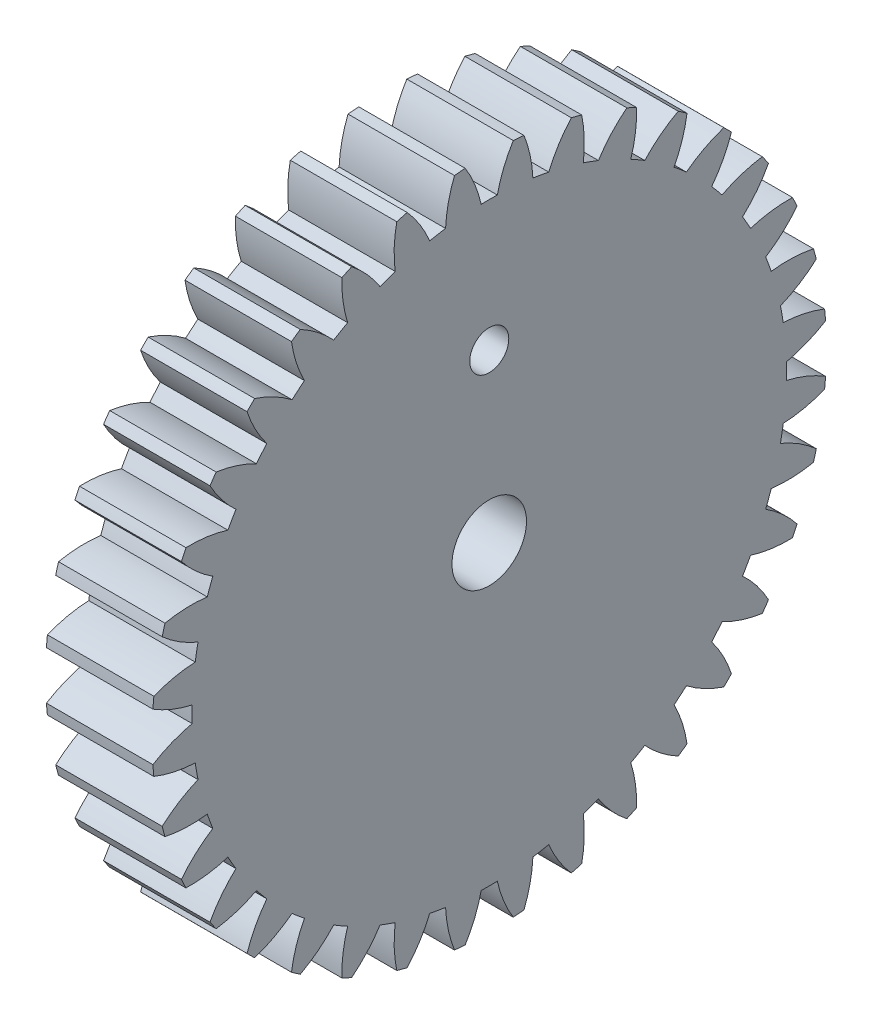
SolidWorks part; units mm, degrees
ref_plane "Plane1" through (0, 0, 0) normal (0, 0, 1) x (1, 0, 0)
ref_plane "Plane2" through (0, 0, 0) normal (0, 1, 0) x (1, 0, 0)
ref_plane "Plane3" through (0, 0, 0) normal (1, 0, 0) x (0, 0, -1)
sketch "HoldingSke" plane through (0, 0, 0) normal (0, 1, 0) x (1, 0, 0)
  line L0 (0, 0) -> (0.809, -0.5878)
  line L1 (-15, 0) -> (100, 0) construction
  line L2 (0, 0) -> (-2.1039, 2.3779)
  line L3 (0, 0) -> (-11.863, 4.5341)
  line L4 (0, 0) -> (6.9867, 5.0761)
  line L5 (0, 0) -> (-46.8476, -17.4728)
  line L6 (0, 0) -> (-5.8027, -3.9151)
  line L7 (-2.1039, 2.3779) -> (8.6586, 51.2059)
  line L8 (-76.2, 54.61) -> (-76.1, 54.61)
  line L9 (-71.009, 38.7566) -> (-53.1078, 45.2721)
  line L10 (-76.2, 71.12) -> (104.1128, 71.12)
  line L11 (0, 0) -> (-7, 0)
  line L12 (-76.2, 101.6) -> (-76.162, 101.6)
  line L13 (24.9733, 27.94) -> (52.9518, 28.4284)
  line L14 (24.9733, 27.94) -> (24.9743, 27.94)
  line L15 (24.9733, 27.94) -> (100.4006, 29.5858)
  line L16 (-63.627, -1) -> (-12.827, -1)
  circle A0 centre (0, 0) radius 0.4
  circle A1 centre (0, 0) radius 16.749
  circle A2 centre (0, 0) radius 37.5
  circle A3 centre (0, 0) radius 0.4
  dimension "MHD" = 33.498
  dimension "Hub_dia" = 75
  dimension "Bore" = 0.8
  dimension "MBD" = 0.8
  dimension "Num_teeth" = 36
  dimension "Pitch_radius" = 180.3128
  dimension "Pitch" = 1
  dimension "Width" = 7
  dimension "Overall_len" = 50
  dimension "Show_teeth" = 36
  dimension "Thickness" = 7
  dimension "OAL" = 50.0001
  dimension "T_dim" = 0.1
  dimension "Ap" = 20
  dimension "H" = 19.05
  dimension "Backlash" = 0.038
  dimension "Addendum_fac" = 1
  dimension "Dedendum_fac" = 1.25
  dimension "Clearance_fac" = 0.25
  dimension "Dedendum_add" = 0.001
  dimension "Module" = 1
sketch "BasProSke" plane through (0, 0, 0) normal (0, 1, 0) x (1, 0, 0)
  line L0 (-10, 0) -> (60, 0) construction
  line L1 (0, 0) -> (0, 19)
  line L2 (0, 0) -> (7, 0)
  line L3 (7, 0) -> (7, 19)
  line L4 (7, 19) -> (0, 19)
  dimension "Diameter" = 38
  dimension "Thickness" = 7
revolve "Base-Revolve" add sketch "BasProSke" angle 360 about L0
sketch "TooCutSke" plane through (0, 0, 0) normal (1, 0, 0) x (0, 0, -1)
  line L1 (0, 0) -> (0, 107) construction
  line L2 (0, 0) -> (-0.8516, 17.9798) construction
  line L3 (0, 0) -> (-3.1351, 35.8344) construction
  line L4 (-0.8516, 17.9798) -> (-1.5676, 17.9172) construction
  arc A0 (0.4547, 16.7428) -> (-0.4547, 16.7428) centre (0, 0) ccw
  arc A1 (1.3689, 18.9761) -> (-1.3689, 18.9761) centre (0, 0) ccw
  circle A2 centre (0, 0) radius 18 construction
  circle A3 centre (0, 0) radius 16.9145 construction
  arc A4 (-0.4547, 16.7428) -> (-1.3689, 18.9761) centre (-7.4808, 15.1702) ccw
  arc A5 (1.3689, 18.9761) -> (0.4547, 16.7428) centre (7.4808, 15.1702) ccw
  dimension "Root_dia" = 33.498
  dimension "Overcut_dia" = 38.0508
  dimension "Pitch_dia" = 36
  dimension "Base_dia" = 33.8289
  dimension "Flank_rad" = 7.2
  dimension "Half_ang" = 5
  dimension "Half_CT" = 0.7186
extrude "ToothCut" cut sketch "TooCutSke" along normal through all
fillet "Breaks" [suppressed] radius 0.02
fillet "RootFillets" [suppressed] radius 0.251
pattern_circular "TeethCuts" count 36 every 10 about axis through (-10, 0, 0) along (1, 0, 0) of "ToothCut", "RootFillets", "Breaks"
sketch "HubNeaOneSke" plane through (0, 0, 0) normal (-1, 0, 0) x (0, 0, 1)
  circle A0 centre (0, 0) radius 16.749
  dimension "Diameter" = 33.498
extrude "HubNearOne" [suppressed] add sketch "HubNeaOneSke" along normal blind 43.0001
sketch "HubNeaBotSke" plane through (0, 0, 0) normal (-1, 0, 0) x (0, 0, 1)
  circle A0 centre (0, 0) radius 16.749
  dimension "Diameter" = 33.498
extrude "HubNearBoth" [suppressed] add sketch "HubNeaBotSke" along normal blind 21.5
ref_plane "FarPln" through (7, 0, 0) normal (1, 0, 0) x (0, 0, -1)
sketch "HubFarSke" plane through (7, 0, 0) normal (1, 0, 0) x (0, 0, -1)
  circle A0 centre (0, 0) radius 16.749
  dimension "Diameter" = 33.498
extrude "HubFar" [suppressed] add sketch "HubFarSke" along normal blind 21.5
sketch "BorSke" plane through (0, 0, 0) normal (1, 0, 0) x (0, 0, -1)
  circle A0 centre (0, 0) radius 0.4
  dimension "Diameter" = 0.8
extrude "Bore" cut sketch "BorSke" along normal mid plane 100.0001
sketch "KeySke" plane through (0, 0, 0) normal (1, 0, 0) x (0, 0, -1)
  line L0 (-0.05, 0) -> (-0.05, 0.5)
  line L1 (-0.05, 0.5) -> (0.05, 0.5)
  line L2 (0.05, 0.5) -> (0.05, 0)
  line L3 (0, 0) -> (0, 34) construction
  line L4 (-0.05, 0) -> (0.05, 0)
  dimension "Offset" = 0.5
  dimension "Width" = 0.1
extrude "Keyway" [suppressed] cut sketch "KeySke" along normal mid plane 100.0001
pattern_circular "Keyway2" [suppressed] count 2 every 90 about axis through (-10, 0, 0) along (1, 0, 0)
sketch "Sketch1" plane through (7, 0, 0) normal (1, 0, 0) x (0, 0, -1)
  circle A0 centre (0, 0) radius 2.1
sketch "Sketch2" plane through (7, 0, 0) normal (1, 0, 0) x (0, 0, -1)
  circle A0 centre (0, 9.4) radius 1.1
  dimension "D1" = 9.4
extrude "Cut-Extrude1" cut sketch "Sketch1" against normal blind 10 contours A0
extrude "Cut-Extrude2" cut sketch "Sketch2" against normal blind 10 contours A0
sketch "Sketch3" plane through (0, 0, 0) normal (-1, 0, 0) x (0, 0, 1)
  circle A0 centre (0, 0) radius 24.3703
extrude "Cut-Extrude3" cut sketch "Sketch3" against normal blind 1 contours A0
equation "' \"Module@HoldingSke\" = 6.35"
equation "' \"Num_teeth@HoldingSke\" = 12"
equation "' \"Ap@HoldingSke\" =  20"
equation "' \"Width@HoldingSke\" = 0.5 * 25.4"
equation "' \"Hub_dia@HoldingSke\"= 1 * 25.4"
equation "' \"Overall_len@HoldingSke\" = 1.0 * 25.4"
equation "' \"Bore@HoldingSke\" = 0.75 * 25.4"
equation "' \"T_dim@HoldingSke\" = 0.1 * 25.4"
equation "' \"Width@KeySke\" = 0.25 * 25.4"
equation "' \"Show_teeth@HoldingSke\" = 13"
equation "' \"Backlash@HoldingSke\" = 0.009 * 25.4"
equation "' \"Addendum_fac@HoldingSke\" = 1.0"
equation "' \"Dedendum_fac@HoldingSke\" = 1.25"
equation "' \"Dedendum_add@HoldingSke\" = 0.00005 * 25.4"
equation "' \"Clearance_fac@HoldingSke\" = 0.25"
equation "\"Pitch@HoldingSke\" = 1 / \"Module@HoldingSke\""
equation "\"Overcut_dia@TooCutSke\" = (\"Num_teeth@HoldingSke\" + 2 * \"Addendum_fac@HoldingSke\") / \"Pitch@HoldingSke\" + 0.002 * 25.4"
equation "\"Pitch_dia@TooCutSke\" = \"Num_teeth@HoldingSke\" / \"Pitch@HoldingSke\""
equation "\"Base_dia@TooCutSke\" = \"Num_teeth@HoldingSke\" / \"Pitch@HoldingSke\" * cos((\"Ap@HoldingSke\"  * 3.14159265 / 180))"
equation "\"Root_dia@TooCutSke\" = (\"Num_teeth@HoldingSke\" + 2) / \"Pitch@HoldingSke\" - 2 * (\"Addendum_fac@HoldingSke\" + \"Dedendum_fac@HoldingSke\") / \"Pitch@HoldingSke\" - \"Dedendum_add@HoldingSke\" * 2"
equation "\"Half_ang@TooCutSke\" = 180 / \"Num_teeth@HoldingSke\""
equation "\"Half_CT@TooCutSke\" = \"Num_teeth@HoldingSke\" / \"Pitch@HoldingSke\" * sin((3.14159265 / 2 / \"Num_teeth@HoldingSke\")) / 2 - 7 * \"Backlash@HoldingSke\" / 4"
equation "\"Flank_rad@TooCutSke\" = \"Num_teeth@HoldingSke\" / \"Pitch@HoldingSke\" / 5"
equation "\"Radius@RootFillets\" = \"Clearance_fac@HoldingSke\" / \"Pitch@HoldingSke\" + \"Dedendum_add@HoldingSke\""
equation "\"Break_rad@Breaks\" = 0.02 / \"Pitch@HoldingSke\""
equation "\"Thickness@HoldingSke\" = \"Width@HoldingSke\""
equation "\"OAL@HoldingSke\" = \"Thickness@HoldingSke\""
equation "\"MHD@HoldingSke\" = (\"Num_teeth@HoldingSke\" + 2) / \"Pitch@HoldingSke\" - 2 * (\"Addendum_fac@HoldingSke\" + \"Dedendum_fac@HoldingSke\")  / \"Pitch@HoldingSke\" - \"Dedendum_add@HoldingSke\" * 2"
equation "\"MBD@HoldingSke\" = (\"Num_teeth@HoldingSke\" + 2) / \"Pitch@HoldingSke\" - 2 * (\"Addendum_fac@HoldingSke\" + \"Dedendum_fac@HoldingSke\")  / \"Pitch@HoldingSke\" - \"Dedendum_add@HoldingSke\" * 2 - 0.002 * 25.4"
equation "\"MHD@HoldingSke\" = ((sgn( \"MHD@HoldingSke\" - \"Hub_dia@HoldingSke\" )-1)*( \"MHD@HoldingSke\" - \"Hub_dia@HoldingSke\" ))/-2+ \"Hub_dia@HoldingSke\""
equation "\"MBD@HoldingSke\" = ((sgn( \"MBD@HoldingSke\" - \"Bore@HoldingSke\" )-1)*( \"MBD@HoldingSke\" - \"Bore@HoldingSke\" ))/-2+ \"Bore@HoldingSke\""
equation "\"OAL@HoldingSke\" = ((sgn( \"OAL@HoldingSke\" - \"Overall_len@HoldingSke\" )+1)*( \"OAL@HoldingSke\" - \"Overall_len@HoldingSke\" ))/2 + \"Overall_len@HoldingSke\" + 0.000002 * 25.4"
equation "\"Num_teeth@TeethCuts\" = int( \"Show_teeth@HoldingSke\" ) + 1"
equation "\"Num_teeth@TeethCuts\" = ((sgn( \"Num_teeth@TeethCuts\" - \"Num_teeth@HoldingSke\" )-1)*( \"Num_teeth@TeethCuts\" - \"Num_teeth@HoldingSke\" ))/-2+ \"Num_teeth@HoldingSke\""
equation "\"Num_teeth@TeethCuts\" = ((sgn( \"Num_teeth@TeethCuts\" - 2.0)+1)*( \"Num_teeth@TeethCuts\" - 2.0))/2 +2.0"
equation "\"Angle@TeethCuts\" = 360.0 / \"Num_teeth@HoldingSke\""
equation "\"Diameter@BasProSke\" = (\"Num_teeth@HoldingSke\" + 2 * \"Addendum_fac@HoldingSke\") / \"Pitch@HoldingSke\""
equation "\"Thickness@BasProSke\"  = \"Thickness@HoldingSke\""
equation "' \"Fillet_rad@BasProSke\" =  \"Thickness@HoldingSke\" * 0.05"
equation "\"MHD@HoldingSke\" = ((sgn( \"MHD@HoldingSke\" - \"Root_dia@TooCutSke\" )-1)*( \"MHD@HoldingSke\" - \"Root_dia@TooCutSke\" ))/-2+ \"Root_dia@TooCutSke\""
equation "\"Diameter@HubNeaOneSke\" = \"MHD@HoldingSke\""
equation "\"Length@HubNearOne\" = \"OAL@HoldingSke\" - \"Thickness@BasProSke\""
equation "\"Diameter@HubNeaBotSke\" = \"MHD@HoldingSke\""
equation "\"Length@HubNearBoth\" = ( \"OAL@HoldingSke\" - \"Thickness@BasProSke\" ) / 2.0"
equation "\"Thickness@FarPln\" = \"Thickness@BasProSke\""
equation "\"Diameter@HubFarSke\" = \"MHD@HoldingSke\""
equation "\"Length@HubFar\" = ( \"OAL@HoldingSke\" - \"Thickness@BasProSke\" ) / 2.0"
equation "\"Diameter@BorSke\" = \"MBD@HoldingSke\""
equation "\"D1@Bore\" = \"OAL@HoldingSke\" * 2.0"
equation "\"D1@Keyway\" = \"OAL@HoldingSke\" * 2.0"
equation "\"Offset@KeySke\" = \"T_dim@HoldingSke\" + \"MBD@HoldingSke\" / 2.0"
